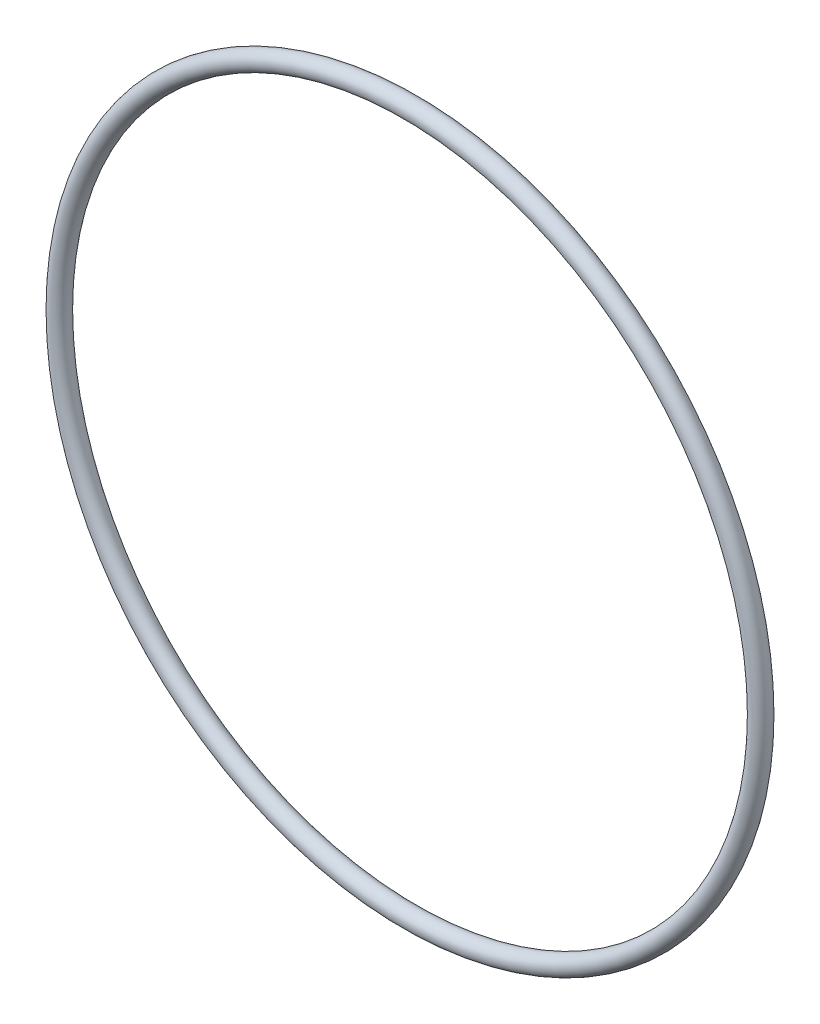
SolidWorks part; units mm, degrees
ref_plane "Front" through (0, 0, 0) normal (0, 0, 1) x (1, 0, 0)
ref_plane "Top" through (0, 0, 0) normal (0, 1, 0) x (1, 0, 0)
ref_plane "Right" through (0, 0, 0) normal (1, 0, 0) x (0, 0, -1)
sketch "Sketch1" plane through (0, 0, 0) normal (1, 0, 0) x (0, -1, 0)
  line L0 (0, -1.3081) -> (0, 1.3081) construction
  line L2 (-55.0837, 0) -> (55.0837, 0) construction
  line L3 (-47.4599, 0) -> (47.4599, 0) construction
  circle A0 centre (48.768, 0) radius 1.3081
  point P9 (47.4599, 0)
  point P10 (50.0761, 0)
  point P13 (48.768, 1.3081)
  point P14 (48.768, -1.3081)
  dimension "Width" = 2.6162
  dimension "ID" = 94.9198
revolve "Revolve1" add sketch "Sketch1" angle 360 about L0
